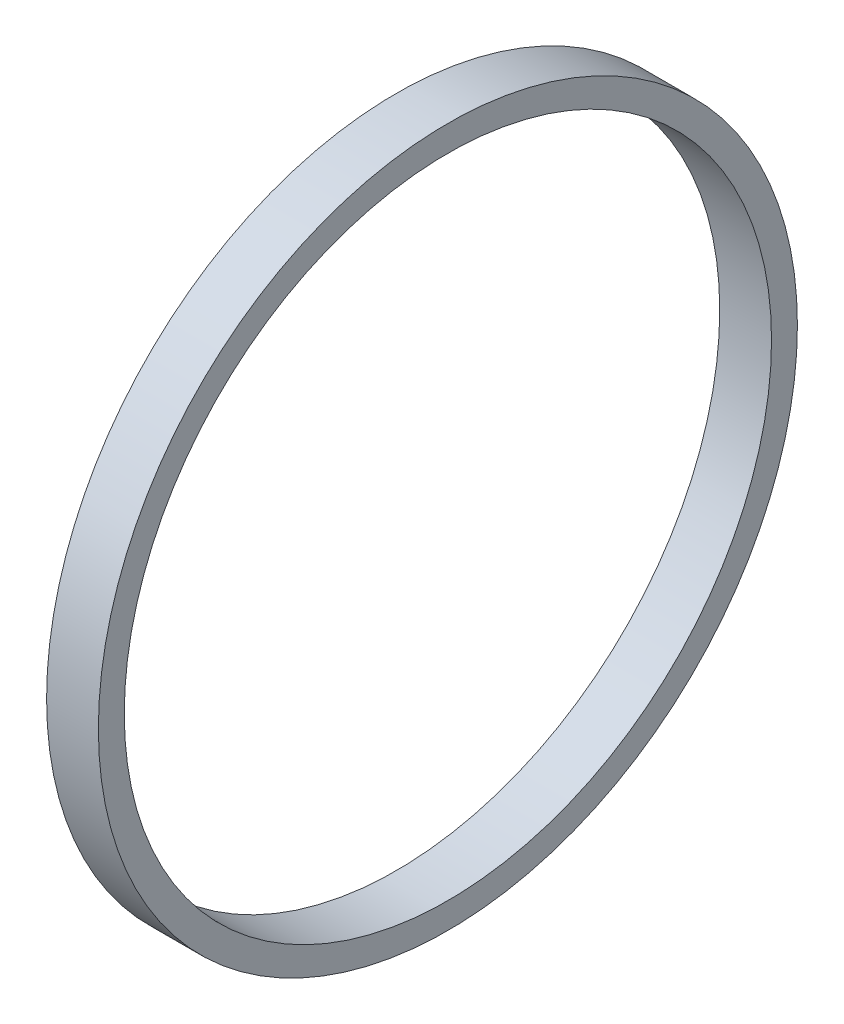
SolidWorks part; units mm, degrees
material "6061 Alloy"
ref_plane "前基準面" through (0, 0, 0) normal (0, 0, 1) x (1, 0, 0)
ref_plane "上基準面" through (0, 0, 0) normal (0, 1, 0) x (1, 0, 0)
ref_plane "右基準面" through (0, 0, 0) normal (1, 0, 0) x (0, 0, -1)
sketch "Sketch1" plane through (0, 0, 0) normal (1, 0, 0) x (0, 0, -1)
  circle A0 centre (0, 0) radius 12.5
  circle A1 centre (0, 0) radius 13.5
  dimension "D1" = 25
  dimension "D2" = 27
extrude "Boss-Extrude1" add sketch "Sketch1" along normal blind 2
